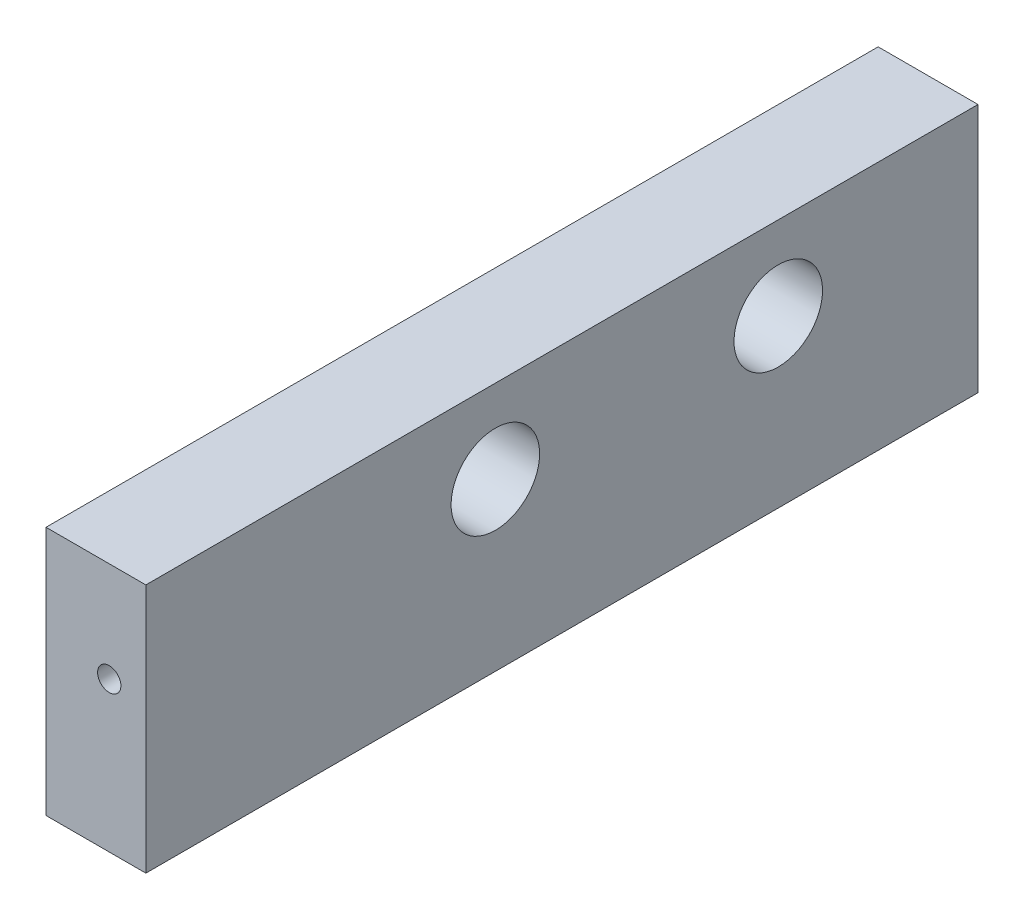
SolidWorks part; units mm, degrees
ref_plane "Front Plane" through (0, 0, 0) normal (0, 0, 1) x (1, 0, 0)
ref_plane "Top Plane" through (0, 0, 0) normal (0, 1, 0) x (1, 0, 0)
ref_plane "Right Plane" through (0, 0, 0) normal (1, 0, 0) x (0, 0, -1)
sketch "Sketch1" plane through (0, 0, 0) normal (0, 0, 1) x (1, 0, 0)
  line L1 (0, 0) -> (7.62, 0)
  line L2 (0, 0) -> (0, 19.05)
  line L3 (0, 19.05) -> (7.62, 19.05)
  line L4 (7.62, 0) -> (7.62, 19.05)
  dimension "D1" = 7.62
  dimension "D2" = 19.05
extrude "Boss-Extrude1" add sketch "Sketch1" against normal blind 63.5
sketch "Sketch2" plane through (0, 0, 0) normal (0, 0, 1) x (1, 0, 0)
  line L0 (0, 19.05) -> (0, 0) construction
  line L1 (0, 0) -> (7.62, 0) construction
  circle A0 centre (4.826, 11.43) radius 0.889
  dimension "D3" = 1.778
  dimension "D1" = 4.826
  dimension "D2" = 11.43
extrude "Cut-Extrude1" cut sketch "Sketch2" against normal blind 6.35
sketch "Sketch3" plane through (0, 0, 0) normal (-1, 0, 0) x (0, 0, 1)
  line L0 (-63.5, 19.05) -> (-63.5, 0) construction
  line L1 (-63.5, 0) -> (0, 0) construction
  circle A0 centre (-48.26, 12.7) radius 3.3782
  dimension "D1" = 6.7564
  dimension "D2" = 15.24
  dimension "D3" = 12.7
extrude "Cut-Extrude2" cut sketch "Sketch3" against normal through all
sketch "Sketch4" plane through (0, 0, 0) normal (-1, 0, 0) x (0, 0, 1)
  line L0 (-63.5, 0) -> (0, 0) construction
  line L1 (-63.5, 19.05) -> (-63.5, 0) construction
  circle A0 centre (-26.67, 12.7) radius 3.3782
  dimension "D2" = 6.7564
  dimension "D1" = 12.7
  dimension "D3" = 36.83
extrude "Cut-Extrude3" cut sketch "Sketch4" against normal through all
